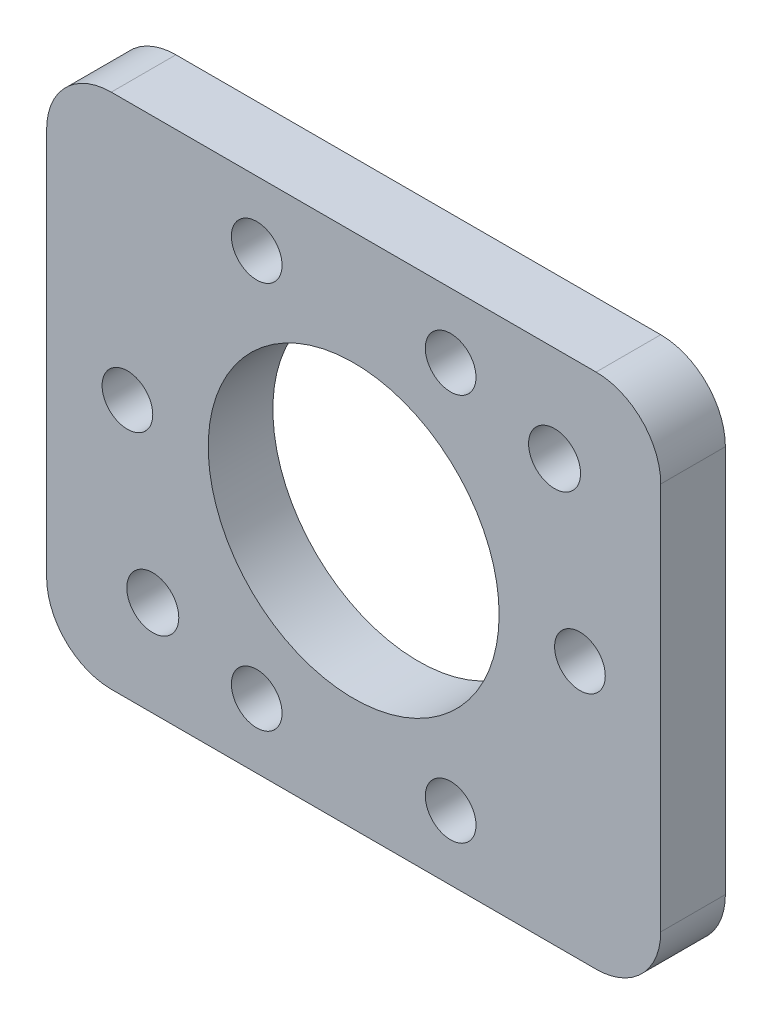
SolidWorks part; units mm, degrees
material "6061-T6 (SS)"
ref_plane "Front Plane" through (0, 0, 0) normal (0, 0, 1) x (1, 0, 0)
ref_plane "Top Plane" through (0, 0, 0) normal (0, 1, 0) x (1, 0, 0)
ref_plane "Right Plane" through (0, 0, 0) normal (1, 0, 0) x (0, 0, -1)
sketch "Sketch1" plane through (0, 0, 0) normal (0, 0, 1) x (1, 0, 0)
  line L0 (-22.225, 0) -> (22.225, 0) construction
  line L1 (-30.1625, 25.4) -> (30.1625, 25.4)
  line L2 (-30.1625, 25.4) -> (-30.1625, -25.4)
  line L3 (-30.1625, -25.4) -> (30.1625, -25.4)
  line L4 (30.1625, 25.4) -> (30.1625, -25.4)
  line L5 (-19.7318, -15.9943) -> (19.7318, 15.9943) construction
  line L6 (-30.1625, 25.4) -> (30.1625, -25.4) construction
  line L7 (-9.525, -19.05) -> (9.525, -19.05) construction
  line L8 (-9.525, -19.05) -> (-9.525, 19.05) construction
  line L9 (-9.525, 19.05) -> (9.525, 19.05) construction
  line L10 (9.525, -19.05) -> (9.525, 19.05) construction
  line L11 (-9.525, -19.05) -> (9.525, 19.05) construction
  line L12 (-9.525, 19.05) -> (9.525, -19.05) construction
  line L13 (-30.1625, -25.4) -> (30.1625, 25.4) construction
  circle A0 centre (0, 0) radius 14.2875
  circle A1 centre (19.7318, 15.9943) radius 2.5527
  circle A2 centre (-19.7318, -15.9943) radius 2.5527
  circle A3 centre (-22.225, 0) radius 2.4892
  circle A4 centre (22.225, 0) radius 2.4892
  circle A5 centre (-9.525, 19.05) radius 2.4892
  circle A6 centre (9.525, 19.05) radius 2.4892
  circle A7 centre (9.525, -19.05) radius 2.4892
  circle A8 centre (-9.525, -19.05) radius 2.4892
  point P11 (0, 0)
  point P13 (0, 0)
  point P17 (0, 25.4)
  point P26 (0, 0)
  point P27 (0, 0)
  point P28 (8.9858, 25.4)
  point P29 (0, 0)
  point P30 (-54.2122, 25.4)
  point P31 (0, 0)
  point P32 (0, 0)
  point P33 (-53.3131, 25.4)
  point P34 (-30.1625, 33.3423)
  point P35 (70.7708, 25.4)
  point P36 (13.2247, -26.6445)
  point P37 (11.6832, 20.3687)
  dimension "D1" = 28.575
  dimension "D3" = 4.9784
  dimension "D4" = 44.45
  dimension "D6" = 5.1054
  dimension "D2" = 50.8
  dimension "D5" = 39.028
  dimension "D7" = 60.325
  dimension "D8" = 50.8
  dimension "D9" = 19.05
  dimension "D10" = 6.35
  dimension "D11" = 19.05
extrude "Boss-Extrude1" add sketch "Sketch1" along normal blind 6.35 contours L4 L1 L2 L3 A8 A7 A6 A5 A4 A3 A2 A1 A0
fillet "Fillet1" radius 6.35 4 edges at (30.1625, 25.4, 3.175) (30.1625, -25.4, 3.175) (-30.1625, -25.4, 3.175) (-30.1625, 25.4, 3.175)
